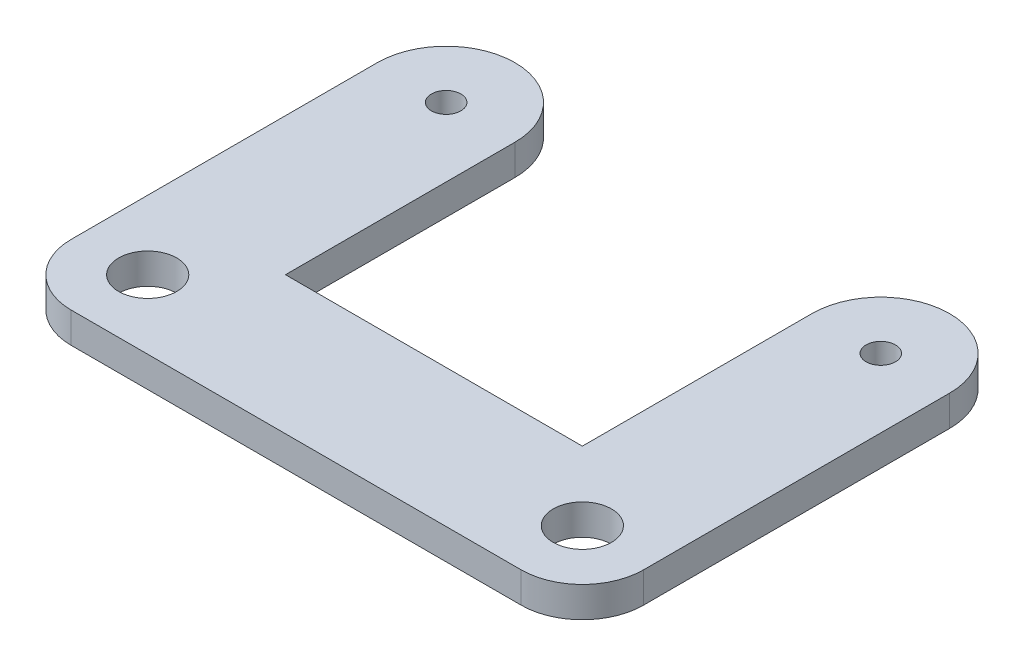
SolidWorks part; units mm, degrees
ref_plane "Front Plane" through (0, 0, 0) normal (0, 0, 1) x (1, 0, 0)
ref_plane "Top Plane" through (0, 0, 0) normal (0, 1, 0) x (1, 0, 0)
ref_plane "Right Plane" through (0, 0, 0) normal (1, 0, 0) x (0, 0, -1)
sketch "Sketch1" plane through (0, 0, 0) normal (0, 1, 0) x (1, 0, 0)
  line L0 (-33.1, 0) -> (-37.9, 0) construction
  line L1 (33.1, 0) -> (37.9, 0) construction
  line L2 (33.1, 0) -> (-33.1, 0) construction
  line L3 (-24.25, 0) -> (-24.25, -37.5)
  line L4 (-24.25, -37.5) -> (24.25, -37.5)
  line L5 (24.25, -37.5) -> (24.25, 0)
  line L6 (-46.75, 0) -> (-46.75, -60)
  line L7 (-46.75, -60) -> (46.75, -60)
  line L8 (46.75, -60) -> (46.75, 0)
  line L12 (-46.75, -60) -> (-24.25, -37.5) construction
  line L13 (24.25, -37.5) -> (46.75, -60) construction
  circle A0 centre (-35.5, 0) radius 2.4
  circle A2 centre (35.5, 0) radius 2.4
  circle A3 centre (-35.5, 0) radius 11.25
  circle A4 centre (35.5, 0) radius 11.25
  circle A5 centre (-35.5, -48.75) radius 4.75
  circle A6 centre (35.5, -48.75) radius 4.75
  dimension "D4" = 22.5
  dimension "D10" = 9.5
  dimension "D2" = 4.8
  dimension "D5" = 37.5
  dimension "D6" = 22.5
  dimension "D7" = 71
extrude "Boss-Extrude1" add sketch "Sketch1" along normal blind 5 contours A4 L5 L4 L3 A3 L6 L7 L8 A6 A5 | A3 A0 | A4 A2
fillet "Fillet1" radius 10 2 edges at (46.75, 2.5, 60) (-46.75, 2.5, 60)
equation "\"m3 hole\"= 3.2"
equation "\"m4 hole\"= 4.2"
equation "\"m5 hole\"= 5.2"
equation "\"m6 hole\"= 6.2"
equation "\"m8 hole\"= 8.2"
equation "\"m3 tapped\"= 2.5"
equation "\"m4 tapped\"= 3.3"
equation "\"m5 tapped\"= 4.2"
equation "\"m6 tapped\"= 5"
equation "\"m8 tapped\"= 6.8"
equation "\"e\"=10"
